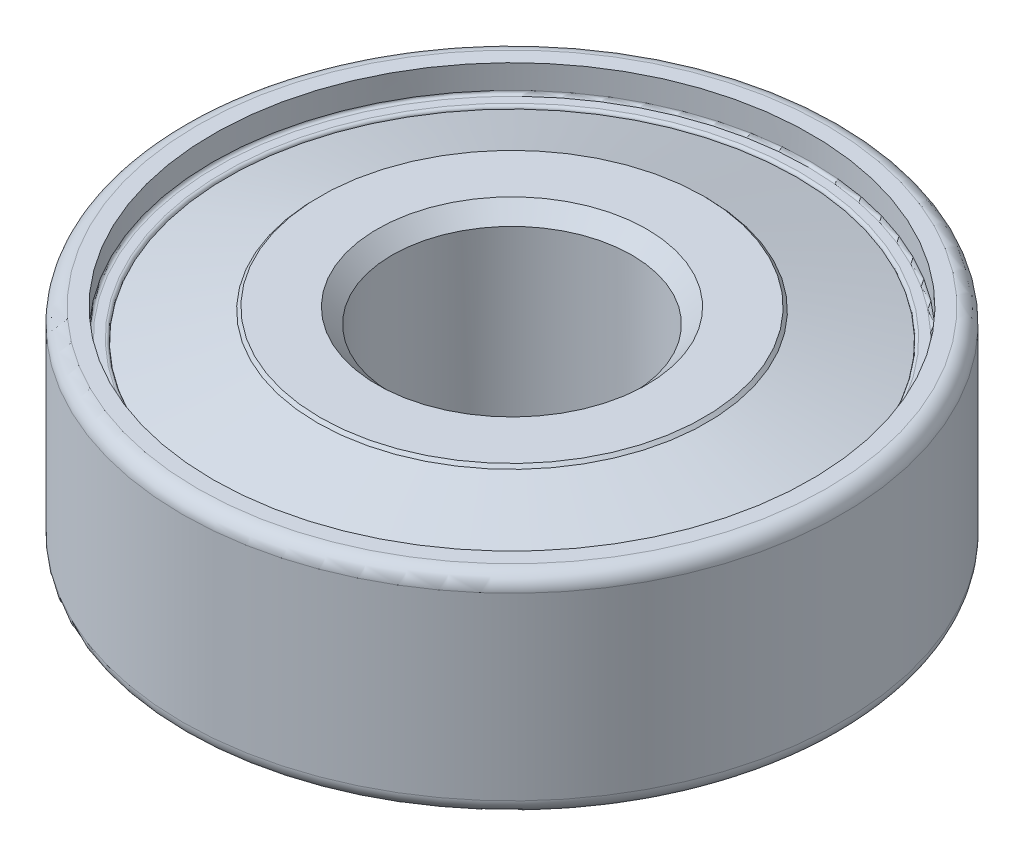
SolidWorks part; units mm, degrees
material "Alloy Steel"
ref_plane "Front Plane" through (0, 0, 0) normal (0, 0, 1) x (1, 0, 0)
ref_plane "Top Plane" through (0, 0, 0) normal (0, 1, 0) x (1, 0, 0)
ref_plane "Right Plane" through (0, 0, 0) normal (1, 0, 0) x (0, 0, -1)
sketch "Sketch1" plane through (0, 0, 0) normal (0, 0, 1) x (1, 0, 0)
  line L0 (0, 0) -> (11, 0) construction
  line L1 (4.5, 0) -> (4.5, 3.5)
  line L2 (4.5, 0) -> (4.5, -3.5)
  line L3 (4.5, 3.5) -> (6.5, 3.5)
  line L4 (4.5, -3.5) -> (6.5, -3.5)
  line L5 (6.5, 3.5) -> (6.5, 1.1)
  line L6 (6.5, -3.5) -> (6.5, -1.1)
  line L7 (6.5, 1.1) -> (9.5, 1.1)
  line L8 (9.5, 1.1) -> (9.5, 2.6)
  line L9 (9.5, 2.6) -> (9.9828, 2.6)
  line L10 (9.9828, 2.6) -> (9.9828, 3.5)
  line L11 (9.9828, 3.5) -> (11, 3.5)
  line L12 (6.5, -1.1) -> (9.5, -1.1)
  line L13 (9.5, -1.1) -> (9.5, -2.6)
  line L14 (9.5, -2.6) -> (9.9828, -2.6)
  line L15 (9.9828, -2.6) -> (9.9828, -3.5)
  line L16 (9.9828, -3.5) -> (11, -3.5)
  line L17 (11, -3.5) -> (11, 3.5)
  line L18 (8, 1.1) -> (8, -1.1) construction
  line L19 (9.9828, 2.6) -> (9.9828, -2.6) construction
  line L20 (0, 3.5) -> (0, -3.5) construction
  arc A0 (9.9828, 0) -> (6.0172, 0) centre (8, 0) ccw
  dimension "D1" = 4.5
sketch "Sketch3" plane through (0, 0, 0) normal (0, 0, 1) x (1, 0, 0)
  line L0 (4, -3.5) -> (4, 3.5)
  line L1 (4, 3.5) -> (6.5, 3.5)
  line L2 (6.5, 3.5) -> (6.5, 1.1)
  line L3 (6.5, 1.1) -> (9.5, 1.1)
  line L4 (9.5, 1.1) -> (9.5, 2.6)
  line L5 (9.5, 2.6) -> (9.9828, 2.6)
  line L6 (9.9828, 2.6) -> (9.9828, 3.5)
  line L7 (9.9828, 3.5) -> (11, 3.5)
  line L8 (11, 3.5) -> (11, -3.5)
  line L9 (11, -3.5) -> (9.9828, -3.5)
  line L10 (9.9828, -3.5) -> (9.9828, -2.6)
  line L11 (9.9828, -2.6) -> (9.5, -2.6)
  line L12 (9.5, -2.6) -> (9.5, -1.1)
  line L13 (9.5, -1.1) -> (6.5, -1.1)
  line L14 (6.5, -1.1) -> (6.5, -3.5)
  line L15 (6.5, -3.5) -> (4, -3.5)
  line L16 (0, 3.5) -> (0, -3.5) construction
  dimension "D1" = 4
revolve "Revolve1" add sketch "Sketch3" angle 360 about L16
sketch "Sketch6" plane through (0, 0, 0) normal (0, 0, 1) x (1, 0, 0)
  line L0 (0, 0) -> (4.5, 0) construction
  line L1 (6.0172, 0) -> (9.9828, 0)
  arc A0 (9.9828, 0) -> (6.0172, 0) centre (8, 0) ccw
fillet "Fillet2" radius 0.1 4 edges at (0, -2.6, 9.9828) (0, -2.6, 9.5) (0, 2.6, 9.9828) (0, 2.6, 9.5)
fillet "Fillet5" radius 0.5 2 edges at (0, -3.5, 11) (0, 3.5, 11)
chamfer "Chamfer1" distance 0.5 angle 45 2 edges at (0, 3.5, 4) (0, -3.5, 4)
chamfer "Chamfer2" distance 0.1 angle 45 2 edges at (0, -3.5, 6.5) (0, 3.5, 6.5)
sketch "Sketch10" plane through (0, -1.1, 0) normal (0, -1, 0) x (1, 0, 0)
  line L0 (0, 6.5) -> (0, 9.5) construction
  line L1 (0, 9.5) -> (0, 8.9) construction
  line L2 (0, 6.5) -> (0, 7.1) construction
  circle A0 centre (0, 0) radius 6.5 construction
  circle A1 centre (0, 0) radius 9.5 construction
  circle A2 centre (0, 0) radius 8.9
  circle A3 centre (0, 0) radius 9.5
  dimension "D1" = 0.6
  dimension "D2" = 0.6
extrude "Cut-Extrude3" cut sketch "Sketch10" against normal through all
sketch "Sketch12" plane through (0, -1.1, 0) normal (0, -1, 0) x (1, 0, 0)
  circle A0 centre (0, 0) radius 6.5
  circle A1 centre (0, 0) radius 7.1
extrude "Cut-Extrude4" cut sketch "Sketch12" against normal through all
revolve "Revolve7" add sketch "Sketch6" angle 360 about L0
pattern_circular "CirPattern2" count 7 over 360 about axis through (0, 0, 0) along (0, 1, 0) of "Revolve7"
surface "Surface-Loft2"
surface "Surface-Loft3"
